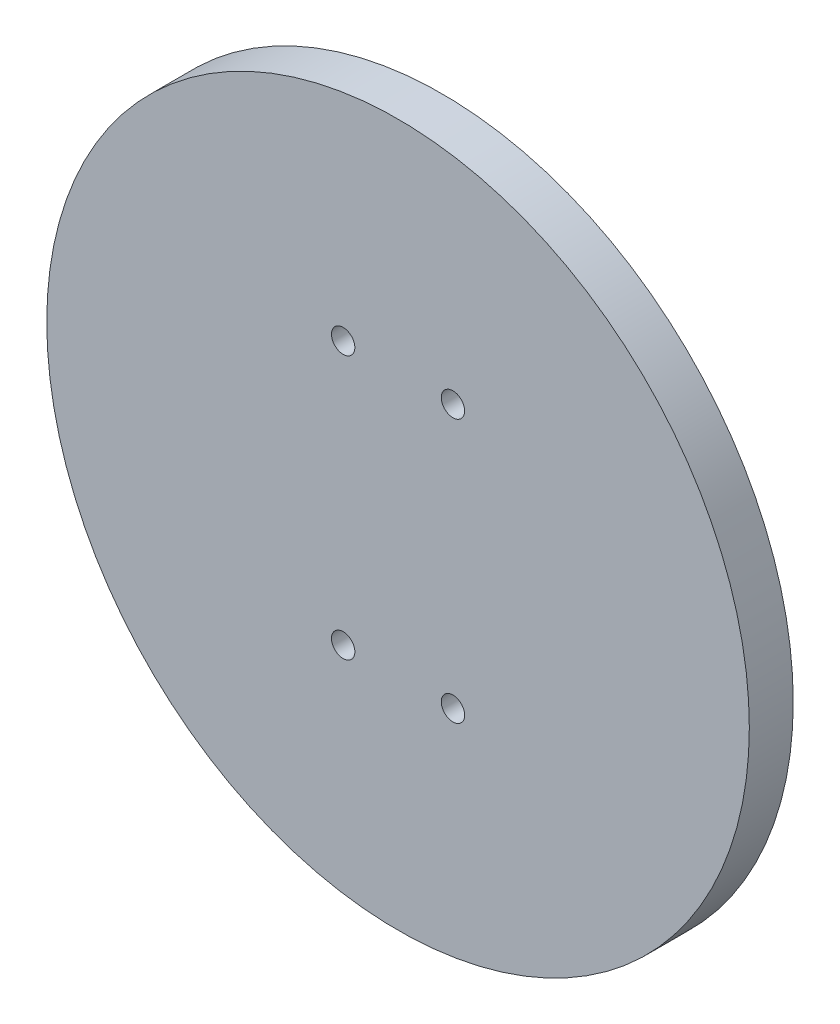
SolidWorks part; units mm, degrees
ref_plane "Front Plane" through (0, 0, 0) normal (0, 0, 1) x (1, 0, 0)
ref_plane "Top Plane" through (0, 0, 0) normal (0, 1, 0) x (1, 0, 0)
ref_plane "Right Plane" through (0, 0, 0) normal (1, 0, 0) x (0, 0, -1)
sketch "Sketch1" plane through (0, 0, 0) normal (0, 0, 1) x (1, 0, 0)
  circle A0 centre (0, 0) radius 101.6
  dimension "D1" = 203.2
extrude "Boss-Extrude1" add sketch "Sketch1" along normal blind 12.7
hole_wizard "CSK for 1/4 Flat Head Machine Screw (100)1" positions "Sketch2" profile "Sketch3" countersink size "1/4" standard "ANSI Inch"
sketch "Sketch2" plane through (0, 0, 0) normal (0, 0, -1) x (-1, 0, 0)
  circle A0 centre (-15.875, -38.1) radius 2.5527 construction
  circle A1 centre (15.875, -38.1) radius 2.5527 construction
  circle A2 centre (-15.875, 38.1) radius 2.5527 construction
  circle A3 centre (15.875, 38.1) radius 2.5527 construction
  point P0 (-15.875, -38.1)
  point P2 (-15.875, 38.1)
  point P4 (15.875, 38.1)
  point P6 (15.875, -38.1)
  point P10 (0, 0)
  point P11 (-13.8432, 55.9654)
  point P12 (0, 0)
  point P15 (0, 0)
  point P18 (0, 0)
  point P21 (0, 0)
sketch "Sketch3" plane through (15.875, -38.1, 0) normal (1, 0, 0) x (0, 1, 0)
  line L0 (0, 0) -> (0, 27.4298)
  line L1 (0, 27.4298) -> (3.3782, 25.4)
  line L2 (3.3782, 25.4) -> (3.3782, 2.5682)
  line L3 (3.3782, 2.5682) -> (6.4389, 0)
  line L5 (6.4389, 0) -> (0, 0)
  line L6 (-3.3782, 2.5682) -> (-6.4389, 0) construction
  line L10 (0, 27.4298) -> (-3.3782, 25.4) construction
  line L11 (0, -6.35) -> (0, 107.95) construction
  dimension "Hole Dia." = 6.7564
  dimension "Hole Depth" = 25.4
  dimension "Near C'Sink Dia." = 12.8778
  dimension "Near C'Sink Angle" = 100
  dimension "Drill Angle" = 118
